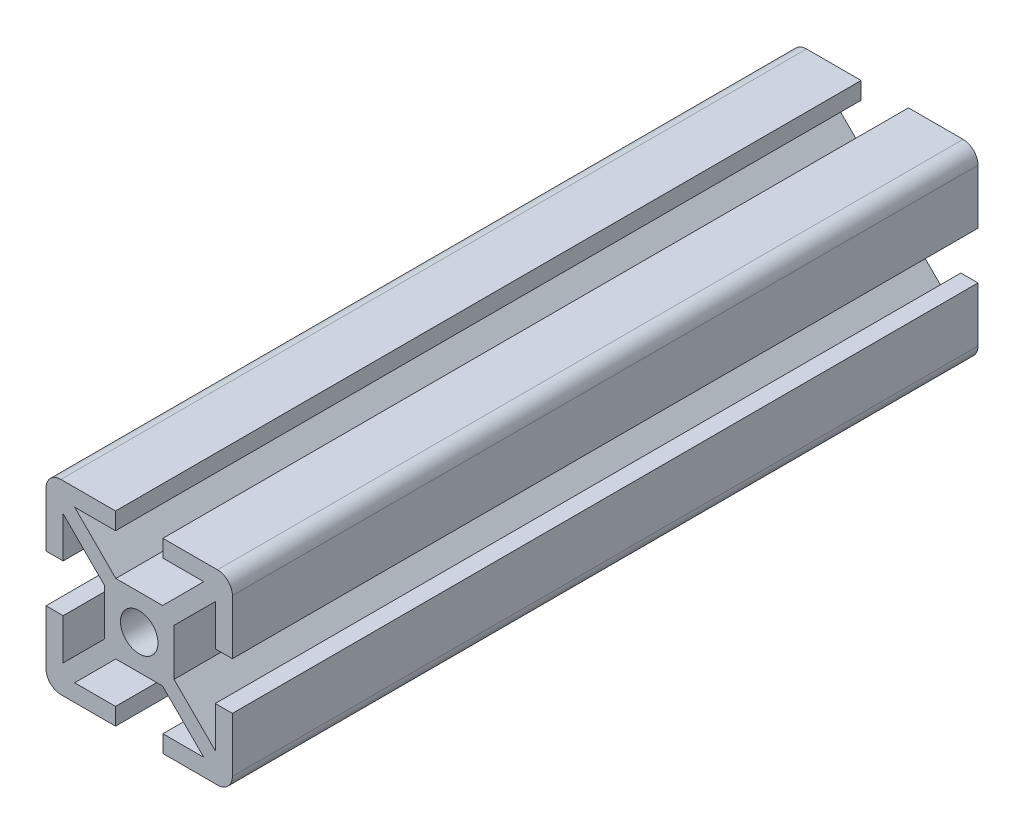
SolidWorks part; units mm, degrees
ref_plane "Front"
ref_plane "Top" through (0, 0, 0) normal (0, 1, 0) x (1, 0, 0)
ref_plane "Right" through (0, 0, 0) normal (1, 0, 0) x (0, 0, -1)
sketch "Sketch1" plane through (0, 0, 0) normal (0, 0, 1) x (1, 0, 0)
  line L0 (0, 0) -> (0, 30.3125) construction
  line L1 (0, 0) -> (-30.9262, 0) construction
  line L2 (-4.7498, 0) -> (-4.7498, 3.1872)
  line L3 (-4.7498, 3.1872) -> (-10.3632, 8.8006)
  line L4 (-10.3632, 8.8006) -> (-10.3632, 3.2258)
  line L5 (3.1872, 4.7498) -> (8.8006, 10.3632)
  line L6 (-12.7, 3.2258) -> (-12.7, 10.668)
  line L7 (0, 4.7498) -> (-3.1872, 4.7498)
  line L8 (-3.1872, 4.7498) -> (-8.8006, 10.3632)
  line L9 (-8.8006, 10.3632) -> (-3.2258, 10.3632)
  line L10 (3.2258, 12.7) -> (10.668, 12.7)
  line L11 (-3.2258, 12.7) -> (-10.668, 12.7)
  line L12 (12.7, 3.2258) -> (12.7, 10.668)
  line L13 (8.8006, 10.3632) -> (3.2258, 10.3632)
  line L14 (10.3632, 8.8006) -> (10.3632, 3.2258)
  line L15 (4.7498, 3.1872) -> (10.3632, 8.8006)
  line L16 (4.7498, 0) -> (4.7498, 3.1872)
  line L17 (4.7498, 0) -> (4.7498, -3.1872)
  line L18 (3.1872, -4.7498) -> (0, -4.7498)
  line L19 (4.7498, -3.1872) -> (10.3632, -8.8006)
  line L20 (10.3632, -8.8006) -> (10.3632, -3.2258)
  line L21 (3.1872, -4.7498) -> (8.8006, -10.3632)
  line L22 (12.7, -3.2258) -> (12.7, -10.668)
  line L23 (-3.2258, -12.7) -> (-10.668, -12.7)
  line L24 (3.2258, -12.7) -> (10.668, -12.7)
  line L25 (8.8006, -10.3632) -> (3.2258, -10.3632)
  line L26 (-3.1872, -4.7498) -> (-8.8006, -10.3632)
  line L27 (0, -4.7498) -> (-3.1872, -4.7498)
  line L28 (-12.7, -3.2258) -> (-12.7, -10.668)
  line L29 (-8.8006, -10.3632) -> (-3.2258, -10.3632)
  line L30 (-10.3632, -8.8006) -> (-10.3632, -3.2258)
  line L31 (-4.7498, -3.1872) -> (-10.3632, -8.8006)
  line L32 (-4.7498, 0) -> (-4.7498, -3.1872)
  line L33 (0, 4.7498) -> (3.1872, 4.7498)
  line L34 (-3.2258, 12.7) -> (-3.2258, 10.3632)
  line L35 (3.2258, 12.7) -> (3.2258, 10.3632)
  line L36 (-10.3632, 3.2258) -> (-12.7, 3.2258)
  line L37 (10.3632, 3.2258) -> (12.7, 3.2258)
  line L38 (-3.2258, -12.7) -> (-3.2258, -10.3632)
  line L39 (-10.3632, -3.2258) -> (-12.7, -3.2258)
  line L40 (10.3632, -3.2258) -> (12.7, -3.2258)
  line L41 (3.2258, -12.7) -> (3.2258, -10.3632)
  arc A0 (-10.668, 12.7) -> (-12.7, 10.668) centre (-10.668, 10.668) ccw
  arc A6 (10.668, 12.7) -> (12.7, 10.668) centre (10.668, 10.668) cw
  arc A13 (10.668, -12.7) -> (12.7, -10.668) centre (10.668, -10.668) ccw
  arc A19 (-10.668, -12.7) -> (-12.7, -10.668) centre (-10.668, -10.668) cw
  circle A20 centre (0, 0) radius 2.5527
  dimension "D2" = 2.032
  dimension "D5" = 2.2098
  dimension "D6" = 9.4742
  dimension "D15" = 5.1054
  dimension "D3" = 7.9502
  dimension "D1" = 45
  dimension "D4" = 7.9502
  dimension "D7" = 9.4742
  dimension "D8" = 5.6134
  dimension "D9" = 12.7
  dimension "D10" = 12.7
  dimension "D11" = 5.6134
extrude "FinalCut" add sketch "Sketch1" against normal blind 101.6
ref_plane "A" through (0, 0, 0) normal (0, 0, 1) x (1, 0, 0)
ref_plane "B" through (0, 0, -101.6) normal (0, 0, -1) x (-1, 0, 0)
ref_plane "Y+" through (0, 12.7, 0) normal (0, 1, 0) x (-1, 0, 0)
ref_plane "X+" through (12.7, 0, 0) normal (1, 0, 0) x (0, 0, -1)
ref_plane "Y-" through (0, -12.7, 0) normal (0, -1, 0) x (1, 0, 0)
ref_plane "X-" through (-12.7, 0, 0) normal (-1, 0, 0) x (0, 0, 1)
ref_plane "SLOT-1-3-" through (0, 0, 0) normal (1, 0, 0) x (0, 0, -1)
ref_plane "SLOT-2-4-" through (0, 0, 0) normal (0, 1, 0) x (-1, 0, 0)
sketch "Sketch18" plane through (0, 0, -101.6) normal (0, 0, -1) x (-1, 0, 0)
  point P0 (0, 0)
sketch "Sketch2" plane through (0, 12.7, 0) normal (0, 1, 0) x (-1, 0, 0)
  line L0 (0, 0) -> (0, -31.9221) construction
  line L1 (3.2258, 0) -> (10.668, 0) construction
  circle A0 centre (0, -10.3124) radius 7.1501
  dimension "D2" = 14.3002
  dimension "D1" = 10.3124
extrude "AFA1" [suppressed] cut sketch "Sketch2" against normal blind 10.668
sketch "Sketch3" plane through (12.7, 0, 0) normal (1, 0, 0) x (0, 0, -1)
  line L0 (0, 0) -> (26.701, 0) construction
  line L1 (0, -3.1872) -> (0, 3.1872) construction
  circle A0 centre (10.3124, 0) radius 7.1501
  dimension "D1" = 14.3002
  dimension "D2" = 10.3124
extrude "AFA2" [suppressed] cut sketch "Sketch3" against normal blind 10.668
sketch "Sketch4" plane through (0, -12.7, 0) normal (0, -1, 0) x (1, 0, 0)
  line L0 (0, 0) -> (0, -27.0117) construction
  line L1 (3.2258, 0) -> (10.668, 0) construction
  circle A0 centre (0, -10.3124) radius 7.1501
  dimension "D1" = 14.3002
  dimension "D2" = 10.3124
extrude "AFA3" [suppressed] cut sketch "Sketch4" against normal blind 10.668
sketch "Sketch5" plane through (-12.7, 0, 0) normal (-1, 0, 0) x (0, 0, 1)
  line L0 (0, 0) -> (-28.9641, 0) construction
  line L1 (0, 10.668) -> (0, 3.2258) construction
  circle A0 centre (-10.3124, 0) radius 7.1501
  dimension "D1" = 14.3002
  dimension "D2" = 10.3124
extrude "AFA4" [suppressed] cut sketch "Sketch5" against normal blind 10.668
sketch "Sketch6" plane through (0, 12.7, 0) normal (0, 1, 0) x (-1, 0, 0)
  line L0 (0, 0) -> (0, -27.1896) construction
  line L1 (-3.1872, -101.6) -> (3.1872, -101.6) construction
  circle A0 centre (0, -91.2876) radius 7.1501
  dimension "D1" = 14.3002
  dimension "D2" = 10.3124
extrude "AFB1" [suppressed] cut sketch "Sketch6" against normal blind 10.668
sketch "Sketch7" plane through (12.7, 0, 0) normal (1, 0, 0) x (0, 0, -1)
  line L0 (0, 0) -> (31.1175, 0) construction
  line L1 (101.6, -3.1872) -> (101.6, 3.1872) construction
  circle A0 centre (91.2876, 0) radius 7.1501
  dimension "D1" = 14.3002
  dimension "D2" = 10.3124
extrude "AFB2" [suppressed] cut sketch "Sketch7" against normal blind 10.668
sketch "Sketch9" plane through (0, -12.7, 0) normal (0, -1, 0) x (1, 0, 0)
  line L0 (0, 0) -> (0, -31.7985) construction
  line L1 (-3.1872, -101.6) -> (3.1872, -101.6) construction
  circle A0 centre (0, -91.2876) radius 7.1501
  dimension "D1" = 14.3002
  dimension "D2" = 10.3124
extrude "AFB3" [suppressed] cut sketch "Sketch9" against normal blind 10.668
sketch "Sketch10" plane through (-12.7, 0, 0) normal (-1, 0, 0) x (0, 0, 1)
  line L0 (0, 0) -> (-27.9391, 0) construction
  line L1 (-101.6, 3.1872) -> (-101.6, -3.1872) construction
  circle A0 centre (-91.2876, 0) radius 7.1501
  dimension "D2" = 14.3002
  dimension "D1" = 10.3124
extrude "AFB4" [suppressed] cut sketch "Sketch10" against normal blind 10.668
sketch "Sketch15" plane through (0, 0, 0) normal (0, 0, 1) x (1, 0, 0)
  circle A3 centre (0, 0) radius 3.3147
  dimension "D1" = 6.6294
extrude "TPA660035" [suppressed] cut sketch "Sketch15" against normal blind 19.05
sketch "Sketch16" plane through (0, 0, -101.6) normal (0, 0, -1) x (-1, 0, 0)
  circle A7 centre (0, 0) radius 3.3147
  dimension "D1" = 6.6294
extrude "TPB660035" [suppressed] cut sketch "Sketch16" against normal blind 19.05
sketch "Sketch23" plane through (0, 0, 0) normal (0, 0, 1) x (1, 0, 0)
  circle A5 centre (0, 0) radius 3.175
  dimension "D1" = 6.35
extrude "TPA660036" [suppressed] cut sketch "Sketch23" against normal blind 25.4
sketch "Sketch24" plane through (0, 0, -101.6) normal (0, 0, -1) x (-1, 0, 0)
  circle A1 centre (0, 0) radius 3.175
  dimension "D1" = 6.35
extrude "TPB660036" [suppressed] cut sketch "Sketch24" against normal blind 25.4
sketch "Sketch11" plane through (0, 0, 0) normal (1, 0, 0) x (0, 0, -1)
  line L0 (0, 12.7) -> (25.4, -12.7)
  line L1 (101.6, -12.7) -> (0, -12.7) construction
  line L2 (101.6, 12.7) -> (0, 12.7) construction
  dimension "D1" = 45
extrude "MITA1" [suppressed] cut sketch "Sketch11" against normal through all and the other way through all flip side to cut
ref_plane "AMITA1" [suppressed] through (0, 6.35, -6.35) normal (0, 0.7071, -0.7071) x (-1, 0, 0)
ref_plane "AMITOFFA1" [suppressed] through (0, 10.8401, -10.8401) normal (0, 0.7071, -0.7071) x (-1, 0, 0)
sketch "Sketch13" [suppressed] plane through (0, 10.8401, -10.8401) normal (0, 0.7071, -0.7071) x (-1, 0, 0)
  line L0 (0, 0) -> (0, -24.9623) construction
  line L1 (3.2258, 8.9803) -> (10.668, 8.9803) construction
  circle A0 centre (0, -8.9775) radius 7.9375
  dimension "D1" = 15.875
  dimension "D2" = 17.9578
extrude "MITCBA1" [suppressed] cut sketch "Sketch13" along normal through all
sketch "Sketch14" [suppressed] plane through (0, 10.8401, -10.8401) normal (0, 0.7071, -0.7071) x (-1, 0, 0)
  line L0 (0, 0) -> (0, -15.592) construction
  line L1 (3.2258, 8.9803) -> (10.668, 8.9803) construction
  circle A0 centre (0, -8.9775) radius 3.2639
  dimension "D1" = 6.5278
  dimension "D2" = 17.9578
extrude "MITDRA1" [suppressed] cut sketch "Sketch14" against normal through all
sketch "Sketch26" [suppressed] plane through (0, 10.8401, -10.8401) normal (0, 0.7071, -0.7071) x (-1, 0, 0)
  line L0 (-7.9375, 8.9803) -> (-7.9375, -8.9775)
  line L1 (7.9375, -8.9775) -> (7.9375, 8.9803)
  line L2 (7.9375, 8.9803) -> (-7.9375, 8.9803)
  line L3 (3.2258, 8.9803) -> (10.668, 8.9803) construction
  arc A0 (-7.9375, -8.9775) -> (7.9375, -8.9775) centre (0, -8.9775) ccw
  dimension "D2" = 7.9375
  dimension "D1" = 17.9578
extrude "MITEBA1" [suppressed] cut sketch "Sketch26" along normal through all
sketch "Sketch27" [suppressed] plane through (0, 10.8401, -10.8401) normal (0, 0.7071, -0.7071) x (-1, 0, 0)
  line L0 (-3.2639, 8.9803) -> (-3.2639, -8.9775)
  line L1 (3.2639, -8.9775) -> (3.2639, 8.9803)
  line L2 (3.2639, 8.9803) -> (-3.2639, 8.9803)
  line L3 (3.2258, 8.9803) -> (10.668, 8.9803) construction
  arc A0 (-3.2639, -8.9775) -> (3.2639, -8.9775) centre (0, -8.9775) ccw
  dimension "D1" = 3.2639
  dimension "D2" = 17.9578
extrude "MITEDA1" [suppressed] cut sketch "Sketch27" against normal through all
sketch "Sketch12" plane through (0, 0, 0) normal (1, 0, 0) x (0, 0, -1)
  line L0 (101.6, 12.7) -> (76.2, -12.7)
  line L1 (101.6, -12.7) -> (0, -12.7) construction
  line L2 (101.6, 12.7) -> (0, 12.7) construction
  dimension "D1" = 45
extrude "MITB1" [suppressed] cut sketch "Sketch12" against normal through all and the other way through all
ref_plane "AMITB1" [suppressed] through (0, -44.45, -44.45) normal (0, 0.7071, 0.7071) x (1, 0, 0)
ref_plane "AMITOFFB1" [suppressed] through (0, -39.9599, -39.9599) normal (0, 0.7071, 0.7071) x (1, 0, 0)
sketch "Sketch21" [suppressed] plane through (0, -39.9599, -39.9599) normal (0, 0.7071, 0.7071) x (1, 0, 0)
  line L5 (10.668, 80.8223) -> (3.2258, 80.8223) construction
  circle A0 centre (0, 62.8645) radius 7.9375
  dimension "D1" = 15.875
  dimension "D2" = 17.9578
extrude "MITCBB1" [suppressed] cut sketch "Sketch21" along normal through all
sketch "Sketch22" [suppressed] plane through (0, -39.9599, -39.9599) normal (0, 0.7071, 0.7071) x (1, 0, 0)
  line L0 (10.668, 80.8223) -> (3.2258, 80.8223) construction
  circle A0 centre (0, 62.8645) radius 3.2639
  dimension "D1" = 17.9578
  dimension "D2" = 6.5278
extrude "MITDRB1" [suppressed] cut sketch "Sketch22" against normal through all
sketch "Sketch28" [suppressed] plane through (0, -39.9599, -39.9599) normal (0, 0.7071, 0.7071) x (1, 0, 0)
  line L0 (-7.9375, 80.8223) -> (-7.9375, 62.8645)
  line L1 (7.9375, 62.8645) -> (7.9375, 80.8223)
  line L2 (7.9375, 80.8223) -> (-7.9375, 80.8223)
  line L3 (10.668, 80.8223) -> (3.2258, 80.8223) construction
  arc A0 (-7.9375, 62.8645) -> (7.9375, 62.8645) centre (0, 62.8645) ccw
  dimension "D1" = 17.9578
  dimension "D2" = 7.9375
extrude "MITEBB1" [suppressed] cut sketch "Sketch28" along normal through all
sketch "Sketch29" [suppressed] plane through (0, -39.9599, -39.9599) normal (0, 0.7071, 0.7071) x (1, 0, 0)
  line L0 (-3.2639, 80.8223) -> (-3.2639, 62.8645)
  line L1 (3.2639, 62.8645) -> (3.2639, 80.8223)
  line L2 (3.2639, 80.8223) -> (-3.2639, 80.8223)
  line L3 (10.668, 80.8223) -> (3.2258, 80.8223) construction
  arc A0 (-3.2639, 62.8645) -> (3.2639, 62.8645) centre (0, 62.8645) ccw
  dimension "D2" = 3.2639
  dimension "D1" = 17.9578
extrude "MITEDB1" [suppressed] cut sketch "Sketch29" against normal through all
sketch "Sketch17" plane through (0, 0, 0) normal (1, 0, 0) x (0, 0, -1)
  line L0 (0, -12.7) -> (25.4, 12.7)
  line L1 (101.6, 12.7) -> (0, 12.7) construction
  line L2 (101.6, -12.7) -> (0, -12.7) construction
  dimension "D1" = 45
extrude "MITA3" [suppressed] cut sketch "Sketch17" against normal through all and the other way through all
ref_plane "AMITA3" [suppressed] through (0, -6.35, -6.35) normal (0, -0.7071, -0.7071) x (-1, 0, 0)
ref_plane "AMITOFFA3" [suppressed] through (0, -10.8401, -10.8401) normal (0, -0.7071, -0.7071) x (-1, 0, 0)
sketch "Sketch30" [suppressed] plane through (0, -10.8401, -10.8401) normal (0, -0.7071, -0.7071) x (-1, 0, 0)
  line L0 (10.668, -8.9803) -> (3.2258, -8.9803) construction
  circle A0 centre (0, 8.9775) radius 7.9375
  dimension "D1" = 15.875
  dimension "D2" = 17.9578
extrude "MITCBA3" [suppressed] cut sketch "Sketch30" along normal through all
sketch "Sketch31" [suppressed] plane through (0, -10.8401, -10.8401) normal (0, -0.7071, -0.7071) x (-1, 0, 0)
  line L0 (10.668, -8.9803) -> (3.2258, -8.9803) construction
  circle A0 centre (0, 8.9775) radius 3.2639
  dimension "D1" = 6.5278
  dimension "D2" = 17.9578
extrude "MITDRA3" [suppressed] cut sketch "Sketch31" against normal through all
sketch "Sketch32" [suppressed] plane through (0, -10.8401, -10.8401) normal (0, -0.7071, -0.7071) x (-1, 0, 0)
  line L0 (-7.9375, -8.9803) -> (-7.9375, 8.9775)
  line L1 (7.9375, 8.9775) -> (7.9375, -8.9803)
  line L2 (7.9375, -8.9803) -> (-7.9375, -8.9803)
  line L3 (10.668, -8.9803) -> (3.2258, -8.9803) construction
  arc A0 (-7.9375, 8.9775) -> (7.9375, 8.9775) centre (0, 8.9775) cw
  dimension "D1" = 7.9375
  dimension "D2" = 17.9578
extrude "MITEBA3" [suppressed] cut sketch "Sketch32" along normal through all
sketch "Sketch33" [suppressed] plane through (0, -10.8401, -10.8401) normal (0, -0.7071, -0.7071) x (-1, 0, 0)
  line L0 (-3.2639, -8.9803) -> (-3.2639, 8.9775)
  line L1 (3.2639, 8.9775) -> (3.2639, -8.9803)
  line L2 (3.2639, -8.9803) -> (-3.2639, -8.9803)
  line L3 (10.668, -8.9803) -> (3.2258, -8.9803) construction
  arc A0 (-3.2639, 8.9775) -> (3.2639, 8.9775) centre (0, 8.9775) cw
  dimension "D1" = 17.9578
  dimension "D2" = 3.2639
extrude "MITEDA3" [suppressed] cut sketch "Sketch33" against normal through all
sketch "Sketch19" plane through (0, 0, 0) normal (1, 0, 0) x (0, 0, -1)
  line L0 (101.6, -12.7) -> (76.2, 12.7)
  line L1 (101.6, -12.7) -> (0, -12.7) construction
  line L2 (101.6, 12.7) -> (0, 12.7) construction
  dimension "D1" = 45
extrude "MITB3" [suppressed] cut sketch "Sketch19" against normal through all and the other way through all flip side to cut
ref_plane "AMITB3" [suppressed] through (0, 44.45, -44.45) normal (0, -0.7071, 0.7071) x (1, 0, 0)
ref_plane "AMITOFFB3" [suppressed] through (0, 39.9599, -39.9599) normal (0, -0.7071, 0.7071) x (1, 0, 0)
sketch "Sketch34" [suppressed] plane through (0, 39.9599, -39.9599) normal (0, -0.7071, 0.7071) x (1, 0, 0)
  line L0 (3.2258, -80.8223) -> (10.668, -80.8223) construction
  circle A0 centre (0, -62.8645) radius 7.9375
  dimension "D1" = 15.875
  dimension "D2" = 17.9578
extrude "MITCBB3" [suppressed] cut sketch "Sketch34" along normal through all
sketch "Sketch35" [suppressed] plane through (0, 39.9599, -39.9599) normal (0, -0.7071, 0.7071) x (1, 0, 0)
  line L1 (3.2258, -80.8223) -> (10.668, -80.8223) construction
  circle A0 centre (0, -62.8645) radius 3.2639
  dimension "D1" = 6.5278
  dimension "D2" = 17.9578
extrude "MITDRB3" [suppressed] cut sketch "Sketch35" against normal through all
sketch "Sketch36" [suppressed] plane through (0, 39.9599, -39.9599) normal (0, -0.7071, 0.7071) x (1, 0, 0)
  line L0 (-7.9375, -80.8223) -> (-7.9375, -62.8645)
  line L1 (7.9375, -62.8645) -> (7.9375, -80.8223)
  line L2 (7.9375, -80.8223) -> (-7.9375, -80.8223)
  line L3 (3.2258, -80.8223) -> (10.668, -80.8223) construction
  arc A0 (-7.9375, -62.8645) -> (7.9375, -62.8645) centre (0, -62.8645) cw
  dimension "D1" = 17.9578
  dimension "D2" = 7.9375
extrude "MITEBB3" [suppressed] cut sketch "Sketch36" along normal through all
sketch "Sketch37" [suppressed] plane through (0, 39.9599, -39.9599) normal (0, -0.7071, 0.7071) x (1, 0, 0)
  line L0 (-3.2639, -80.8223) -> (-3.2639, -62.8645)
  line L1 (3.2639, -62.8645) -> (3.2639, -80.8223)
  line L2 (3.2639, -80.8223) -> (-3.2639, -80.8223)
  line L3 (3.2258, -80.8223) -> (10.668, -80.8223) construction
  arc A0 (-3.2639, -62.8645) -> (3.2639, -62.8645) centre (0, -62.8645) cw
  dimension "D2" = 3.2639
  dimension "D1" = 17.9578
extrude "MITEDB3" [suppressed] cut sketch "Sketch37" against normal through all
